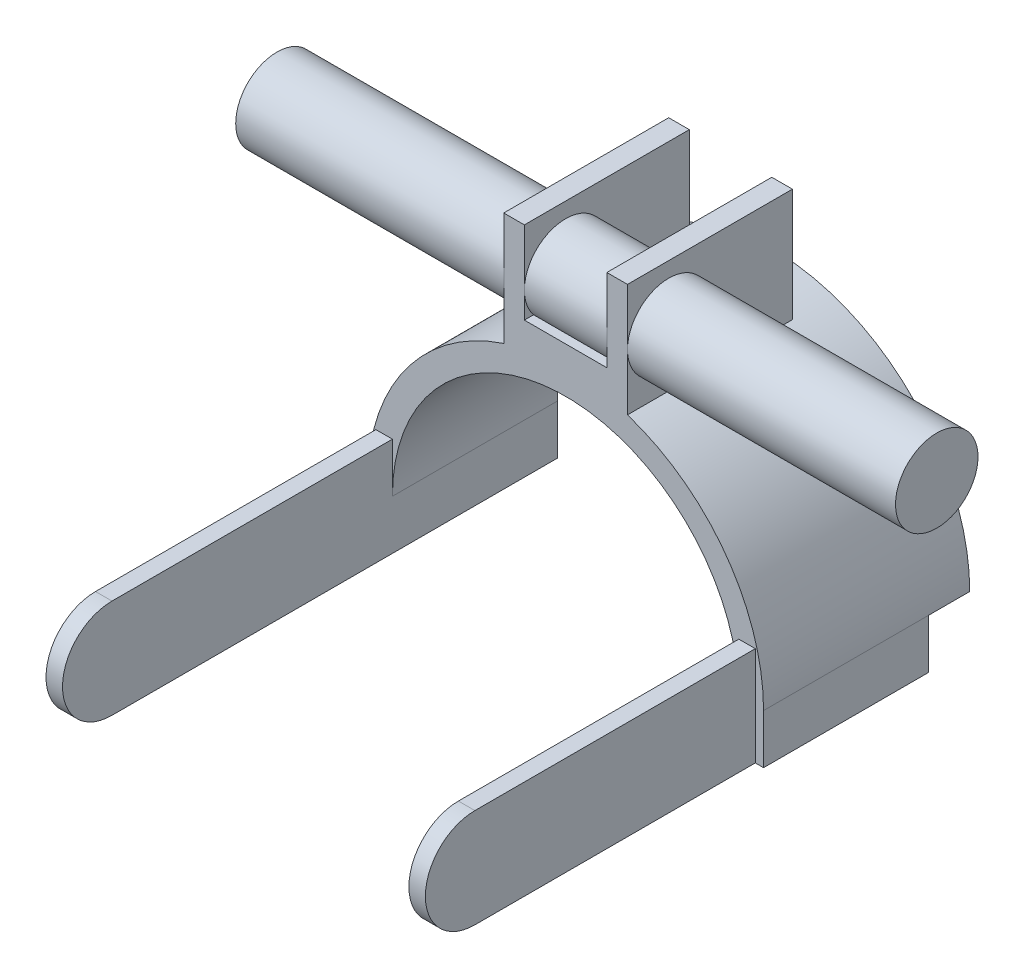
SolidWorks part; units mm, degrees
ref_plane "Front" through (0, 0, 0) normal (0, 0, 1) x (1, 0, 0)
ref_plane "Top" through (0, 0, 0) normal (0, 1, 0) x (1, 0, 0)
ref_plane "Right" through (0, 0, 0) normal (1, 0, 0) x (0, 0, -1)
sketch "草图1" plane through (0, 0, 0) normal (0, 0, 1) x (1, 0, 0)
  line L0 (0, 0) -> (141.2079, 0) construction
  line L1 (0, 164.1608) -> (0, 0) construction
  line L2 (0, 0) -> (-103.3023, 0) construction
  line L3 (-48, 0) -> (-46, 0)
  line L4 (48, 0) -> (46, 0)
  arc A0 (-48, 0) -> (48, 0) centre (0, 0) cw
  arc A1 (-46, 0) -> (46, 0) centre (0, 0) cw
  dimension "D1" = 46
extrude "凸台-拉伸1" add sketch "草图1" along normal blind 10
sketch "草图2" plane through (0, 0, 10) normal (0, 0, 1) x (1, 0, 0)
  line L0 (-46, 0) -> (46, 0) construction
  line L1 (46, 0) -> (48, 0) construction
  line L2 (0, 46) -> (39.0206, 46) construction
  line L4 (-48, 0) -> (-48, -12)
  line L5 (-48, -12) -> (-46, -12)
  line L6 (-46, 0) -> (-46, -12)
  line L8 (46, 0) -> (46, -12)
  line L9 (46, -12) -> (48, -12)
  line L10 (48, 0) -> (48, -12)
  line L11 (-15, 73) -> (-10, 73)
  line L12 (-15, 73) -> (-15, 45.5961)
  line L14 (15, 73) -> (15, 45.5961)
  line L15 (0, 46) -> (-39.5946, 46) construction
  line L16 (0, 46) -> (0, 86.5263) construction
  line L17 (10, 73) -> (15, 73)
  line L19 (-10, 73) -> (-10, 53)
  line L20 (-10, 53) -> (10, 53)
  line L21 (10, 73) -> (10, 53)
  arc A0 (-48, 0) -> (-15, 45.5961) centre (0, 0) cw
  arc A1 (-46, 0) -> (46, 0) centre (0, 0) cw
  arc A2 (15, 45.5961) -> (48, 0) centre (0, 0) cw
  dimension "D1" = 12
  dimension "D2" = 12
  dimension "D3" = 30
  dimension "D4" = 15
  dimension "D7" = 20
  dimension "D8" = 10
  dimension "D9" = 20
extrude "凸台-拉伸2" add sketch "草图2" along normal blind 40
sketch "草图6" plane through (0, 0, 10) normal (0, 0, -1) x (-1, 0, 0)
  line L0 (-46, 0) -> (45.7869, 0) construction
  line L1 (-46, 0) -> (-42.1664, 0)
  line L2 (-42.1664, 0) -> (-42, 0)
  line L3 (42, 0) -> (46, 0)
  arc A0 (-46, 0) -> (46, 0) centre (0, 0) cw
  arc A1 (46, 0) -> (-46, 0) centre (0, 0) ccw construction
  arc A2 (-42, 0) -> (42, 0) centre (0, 0) cw
extrude "凸台-拉伸4" add sketch "草图6" against normal blind 40
sketch "草图7" plane through (0, 0, 10) normal (0, 0, -1) x (-1, 0, 0)
  line L1 (-46, -12) -> (-42, -12)
  line L2 (-46, -12) -> (-46, 12)
  line L3 (-46, 12) -> (-42, 12)
  line L4 (-42, -12) -> (-42, 12)
  line L5 (46, -12) -> (42, -12)
  line L6 (46, -12) -> (46, 12)
  line L7 (46, 12) -> (42, 12)
  line L8 (42, -12) -> (42, 12)
  dimension "D1" = 4
  dimension "D2" = 4
extrude "凸台-拉伸5" add sketch "草图7" against normal blind 120
sketch "草图8" plane through (-46, 0, 0) normal (-1, 0, 0) x (0, 0, 1)
  line L0 (130, -12) -> (130, 12) construction
  line L2 (118, 12) -> (136, 12)
  line L4 (118, -12) -> (136, -12)
  line L5 (136, 12) -> (136, -12)
  arc A0 (118, -12) -> (118, 12) centre (118, 0) ccw
  dimension "D1" = 12
  dimension "D2" = 6
extrude "切除-拉伸3" cut sketch "草图8" against normal through all
sketch "草图10" plane through (0, 0, 0) normal (1, 0, 0) x (0, 0, -1)
  circle A0 centre (-40, 59.298) radius 10
extrude "凸台-拉伸6" add sketch "草图10" along normal mid plane 160
